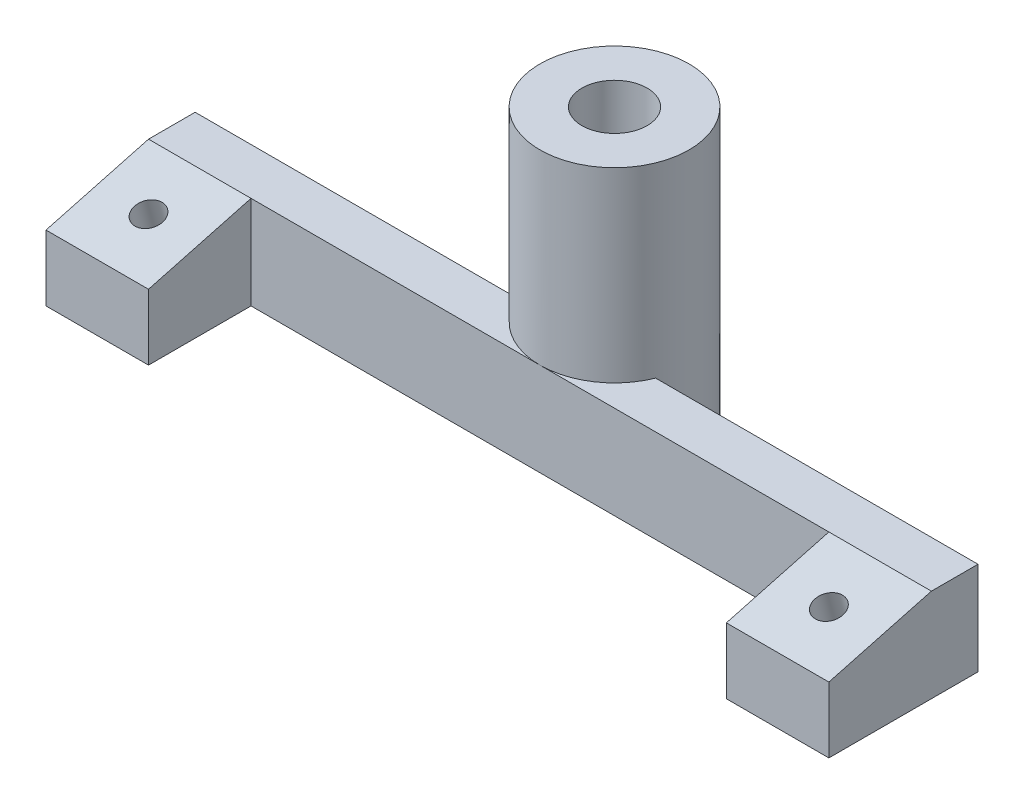
SolidWorks part; units mm, degrees
ref_plane "前视基准面" through (0, 0, 0) normal (0, 0, 1) x (1, 0, 0)
ref_plane "上视基准面" through (0, 0, 0) normal (0, 1, 0) x (1, 0, 0)
ref_plane "右视基准面" through (0, 0, 0) normal (1, 0, 0) x (0, 0, -1)
other "Configuration Table"
sketch "草图1" plane through (0, 0, 0) normal (0, 1, 0) x (1, 0, 0)
  line L0 (-42, 5.5) -> (-42, 10.5)
  line L1 (-31, 5.5) -> (31, 5.5)
  line L2 (-42, 5.5) -> (-42, -5.5)
  line L3 (-42, -5.5) -> (-31, -5.5)
  line L4 (42, 5.5) -> (42, -5.5)
  line L5 (-42, 5.5) -> (42, -5.5) construction
  line L6 (-42, -5.5) -> (42, 5.5) construction
  line L8 (-42, 10.5) -> (42, 10.5)
  line L9 (42, 10.5) -> (42, 5.5)
  line L12 (-31, 5.5) -> (-31, -5.5)
  line L13 (31, -5.5) -> (42, -5.5)
  line L14 (31, 5.5) -> (31, -5.5)
  point P0 (0, 0)
extrude "凸台-拉伸1" add sketch "草图1" along normal blind 10
sketch "草图5" plane through (-42, 0, 0) normal (-1, 0, 0) x (0, 0, 1)
  line L1 (-5.5, 10) -> (5.5, 7.0526)
  line L3 (-5.5, 10) -> (5.5, 10)
  line L4 (5.5, 10) -> (5.5, 7.0526)
extrude "切除-拉伸4" cut sketch "草图5" against normal through all
sketch "草图6" plane through (0, 12.3839, -14.397) normal (0, -0.9659, -0.2588) x (1, 0, 0)
  circle A0 centre (-36.5, 14.9049) radius 1.5
  circle A1 centre (36.5, 14.9049) radius 1.5
  point P0 (36.5, 14.9049)
  point P12 (-36.0834, 14.9049)
extrude "切除-拉伸5" cut sketch "草图6" along normal through all
ref_plane "基准面2" through (0, 4.0914, 1.0963) normal (0, 0.9659, 0.2588) x (1, 0, 0)
sketch "草图7" plane through (0, 4.0914, 1.0963) normal (0, 0.9659, 0.2588) x (1, 0, 0)
  circle A0 centre (-36.5, 2.2068) radius 3.25
  circle A1 centre (36.5, 2.2068) radius 3.25
extrude "切除-拉伸6" cut sketch "草图7" against normal through all
sketch "草图8" plane through (0, 0, 0) normal (0, -1, 0) x (1, 0, 0)
  circle A0 centre (0, -13.5) radius 8
extrude "凸台-拉伸2" add sketch "草图8" against normal blind 30
sketch "草图9" plane through (0, 30, 0) normal (0, 1, 0) x (1, 0, 0)
  circle A0 centre (0, 13.5) radius 3.5
extrude "切除-拉伸7" cut sketch "草图9" against normal blind 30
sketch "草图10" plane through (0, 0, 0) normal (0, -1, 0) x (1, 0, 0)
  circle A0 centre (0, -13.5) radius 5.25
extrude "切除-拉伸8" cut sketch "草图10" against normal blind 24
